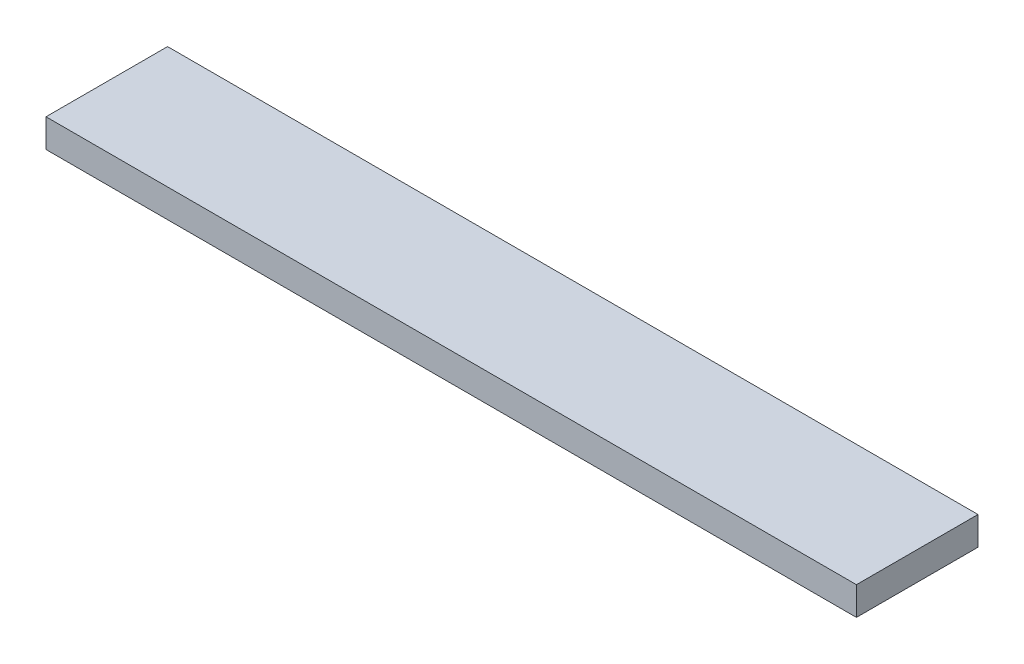
SolidWorks part; units mm, degrees
ref_plane "Front Plane" through (0, 0, 0) normal (0, 0, 1) x (1, 0, 0)
ref_plane "Top Plane" through (0, 0, 0) normal (0, 1, 0) x (1, 0, 0)
ref_plane "Right Plane" through (0, 0, 0) normal (1, 0, 0) x (0, 0, -1)
sketch "Sketch1" plane through (0, 0, 0) normal (0, 0, 1) x (1, 0, 0)
  line L1 (500, 17.5) -> (-500, 17.5)
  line L2 (500, 17.5) -> (500, -17.5)
  line L3 (500, -17.5) -> (-500, -17.5)
  line L4 (-500, 17.5) -> (-500, -17.5)
  line L5 (500, 17.5) -> (-500, -17.5) construction
  line L6 (500, -17.5) -> (-500, 17.5) construction
  point P0 (0, 0)
  dimension "D1" = 1000
  dimension "D2" = 35
extrude "Boss-Extrude1" add sketch "Sketch1" along normal blind 150
